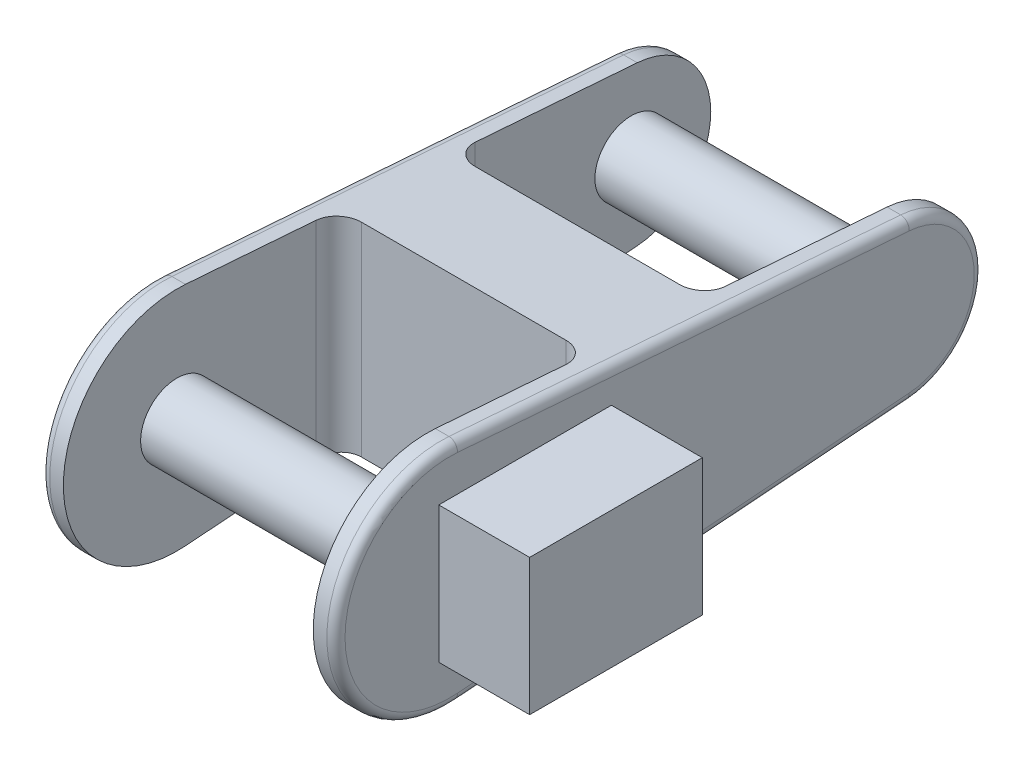
SolidWorks part; units mm, degrees
ref_plane "Front Plane" through (0, 0, 0) normal (0, 0, 1) x (1, 0, 0)
ref_plane "Top Plane" through (0, 0, 0) normal (0, 1, 0) x (1, 0, 0)
ref_plane "Right Plane" through (0, 0, 0) normal (1, 0, 0) x (0, 0, -1)
sketch "Sketch1" plane through (0, 0, 0) normal (1, 0, 0) x (0, 0, -1)
  line L0 (1.875, -24.9296) -> (101.3125, -17.4507)
  line L1 (1.875, 24.9296) -> (101.3125, 17.4507)
  arc A0 (1.875, 24.9296) -> (1.875, -24.9296) centre (0, 0) ccw
  arc A1 (101.3125, -17.4507) -> (101.3125, 17.4507) centre (100, 0) ccw
extrude "Boss-Extrude1" add sketch "Sketch1" along normal mid plane 65
sketch "Sketch2" plane through (0, 0, 0) normal (0, 1, 0) x (1, 0, 0)
  line L5 (-27.5, 117.5) -> (27.5, 117.5)
  line L7 (32.5, 117.5) -> (-32.5, 117.5) construction
  line L8 (-27.5, 117.5) -> (-27.5, 60.6352)
  line L9 (-27.5, 35.6352) -> (-27.5, -25)
  line L10 (-32.5, -25) -> (32.5, -25) construction
  line L11 (27.5, 117.5) -> (27.5, 60.6352)
  line L12 (27.5, 35.6352) -> (27.5, -25)
  line L13 (-27.5, -25) -> (27.5, -25)
  line L14 (-27.5, 60.6352) -> (27.5, 60.6352)
  line L15 (-27.5, 35.6352) -> (27.5, 35.6352)
extrude "Cut-Extrude1" cut sketch "Sketch2" against normal mid plane 65
sketch "Sketch4" plane through (-27.5, 0, 0) normal (1, 0, 0) x (0, 0, -1)
  circle A0 centre (0, 0) radius 8
  circle A1 centre (100, 0) radius 8
  dimension "D1" = 16
  dimension "D2" = 16
extrude "Boss-Extrude2" add sketch "Sketch4" along normal up to surface (55 mm away) up to face at (27.5, 0, -85.0207)
sketch "Sketch5" plane through (32.5, 0, 0) normal (1, 0, 0) x (0, 0, -1)
  line L0 (35.6352, -22.3904) -> (35.6352, 22.3904) construction
  line L1 (-2.3648, -15) -> (35.6352, -15)
  line L3 (-2.3648, 15) -> (35.6352, 15)
  line L4 (35.6352, -15) -> (35.6352, 15)
  line L7 (-2.3648, 15) -> (-2.3648, -15)
  point P0 (0, 0)
  dimension "D1" = 30
  dimension "D2" = 38
extrude "Boss-Extrude3" add sketch "Sketch5" along normal blind 20
sketch "Sketch6" plane through (0, 0, -35.6352) normal (0, 0, -1) x (-1, 0, 0)
  circle A0 centre (-42.5, 8) radius 3
  circle A1 centre (-42.5, -8) radius 3
  dimension "D1" = 6
extrude "Boss-Extrude4" add sketch "Sketch6" along normal blind 3
fillet "Fillet1" radius 2 4 edges at (32.5, 0, -117.5) (32.5, -21.1902, -51.5938) (32.5, 0, 25) (32.5, 21.1902, -51.5938)
fillet "Fillet3" radius 2 4 edges at (-32.5, 0, -117.5) (-32.5, -21.1902, -51.5938) (-32.5, 0, 25) (-32.5, 21.1902, -51.5938)
fillet "Fillet5" radius 5 1 edges at (27.5, 0, -60.6352)
fillet "Fillet6" radius 5 1 edges at (-27.5, 0, -60.6352)
fillet "Fillet7" radius 5 1 edges at (-27.5, 0, -35.6352)
fillet "Fillet8" radius 5 1 edges at (27.5, 0, -35.6352)
sketch "Sketch7" plane through (0, 0, 0) normal (1, 0, 0) x (0, 0, -1)
  point P0 (0, 0)
sketch "Sketch8" plane through (0, 0, 0) normal (1, 0, 0) x (0, 0, -1)
  point P0 (100, 0)
